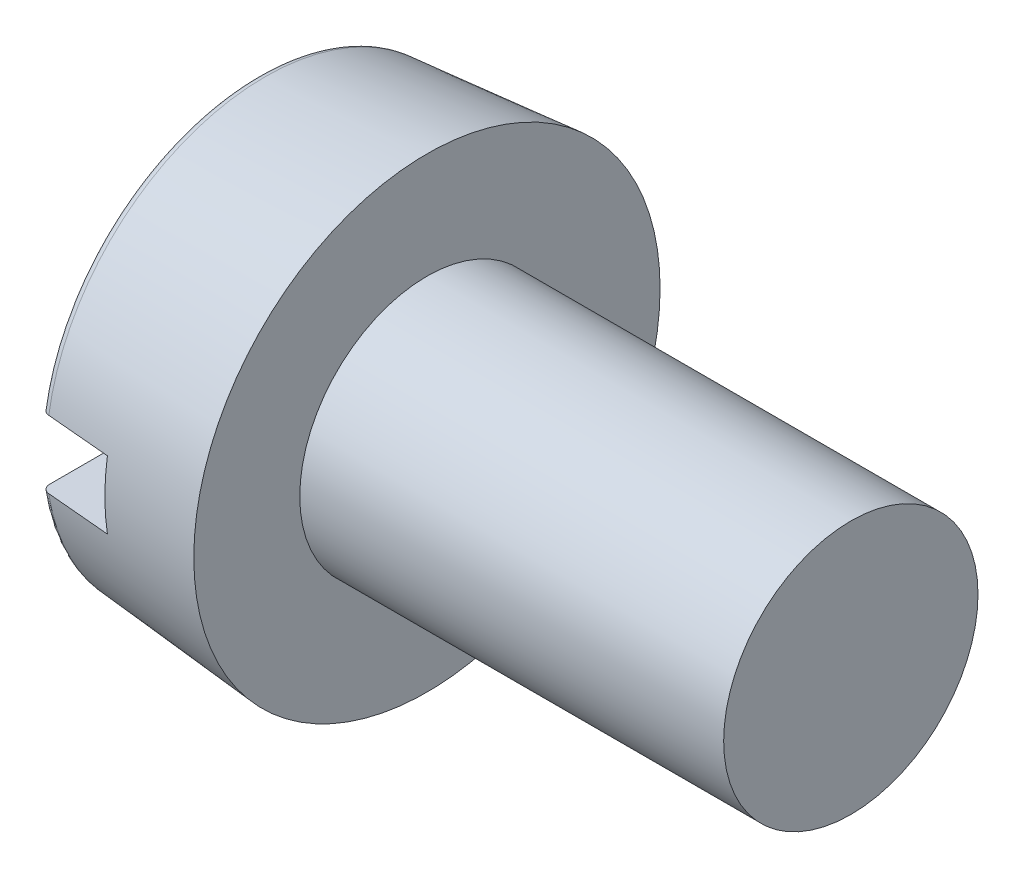
SolidWorks part; units mm, degrees
ref_plane "Plane1" through (0, 0, 0) normal (0, 0, 1) x (1, 0, 0)
ref_plane "Plane2" through (0, 0, 0) normal (0, 1, 0) x (1, 0, 0)
ref_plane "Plane3" through (0, 0, 0) normal (1, 0, 0) x (0, 0, -1)
revolve "Base-Revolve" add sketch "BodySke"
sketch "BodySke" plane through (0, 0, 0) normal (0, 0, 1) x (1, 0, 0)
  line L0 (2, 1.5) -> (2, 2.75)
  line L1 (0, 0) -> (0, 2.575)
  line L2 (-25.4, 0) -> (127, 0) construction
  line L3 (7, 0) -> (0, 0)
  line L4 (2, 1.5) -> (7, 1.5)
  line L5 (7, 1.5) -> (7, 0)
  line L6 (0, 2.575) -> (2, 2.75)
  line L9 (2.5, 3.0875) -> (2.5, -6.4375) construction
  line L10 (2, 6.35) -> (2, -3.175) construction
  dimension "Head_ht" = 2
  dimension "Diameter" = 3
  dimension "Length" = 5
  dimension "Head_dia" = 5.5
  dimension "Advance" = 0.5
  dimension "Thread_nom" = 5
  dimension "Head_side_angle" = 5
cosmetic thread "ThreadCosmetic" [suppressed]
fillet "Fillet1" [suppressed] radius 0.1
fillet "Fillet2" radius 0.1 1 edges at (0, 0, 2.575)
sketch "Sketch2" plane through (0, 0, 0) normal (1, 0, 0) x (0, 0, -1)
  line L0 (2.75, -0.4) -> (-2.75, -0.4)
  line L1 (2.75, -0.4) -> (2.75, 0.4)
  line L2 (-2.75, 0.4) -> (2.75, 0.4)
  line L3 (-2.75, 0.4) -> (-2.75, -0.4)
  dimension "D1" = 5.5
  dimension "D2" = 2.75
  dimension "Slot_width" = 0.8
  dimension "D3" = 0.4
extrude "Slot" cut sketch "Sketch2" along normal blind 0.85
sketch "ThdSchSke" plane through (0, 0, 0) normal (0, 0, 1) x (1, 0, 0)
  line L0 (3, -1.2195) -> (2.8036, -1.5)
  line L1 (3, -1.2195) -> (3.1964, -1.5)
  line L2 (3.1964, -1.5) -> (3.1964, -1.875)
  line L3 (-3.175, 0) -> (5.1513, 0) construction
  line L5 (3.1964, -1.875) -> (2.8036, -1.875)
  line L6 (2.8036, -1.875) -> (2.8036, -1.5)
  dimension "Thread_minor" = 2.439
  dimension "Diameter" = 3
  dimension "Start" = 3
  dimension "SideAngle" = 55
  dimension "VeeAngle" = 70
  dimension "Overcut" = 3.75
revolve "ThreadSchematic" [suppressed] cut sketch "ThdSchSke" angle 360 about L3
pattern_linear "ThdSchPat" [suppressed]
equation "\"D1@Sketch2\" = \"Head_dia@BodySke\""
equation "\"D2@Sketch2\" = \"D1@Sketch2\" / 2"
equation "\"D3@Sketch2\" = \"Slot_width@Sketch2\" / 2"
equation "\"Thread_length@ThreadCosmetic\" = ((sgn( (\"Length@BodySke\" - \"Advance@BodySke\" * 2.0 ) - \"Thread_nom@BodySke\" )-1)*( (\"Length@BodySke\" - \"Advance@BodySke\"  * 2.0) - \"Thread_nom@BodySke\" ))/-2+ \"Thread_nom@BodySke\""
equation "\"Thread_minor@ThdSchSke\" = \"Thread_minor@ThreadCosmetic\""
equation "\"Diameter@ThdSchSke\" = \"Diameter@BodySke\""
equation "\"Overcut@ThdSchSke\" = \"Diameter@BodySke\" * 1.25"
equation "\"Start@ThdSchSke\" = \"Head_ht@BodySke\" + \"Length@BodySke\" - \"Thread_length@ThreadCosmetic\"  '---Non-countersunk---"
equation "\"Num_threads@ThdSchPat\" = int( \"Thread_length@ThreadCosmetic\" / \"Advance@BodySke\" + 0.999 )  + 1"
equation "\"Advance@ThdSchPat\" = \"Thread_length@ThreadCosmetic\" /  (\"Num_threads@ThdSchPat\" - 1) 'relax it"
